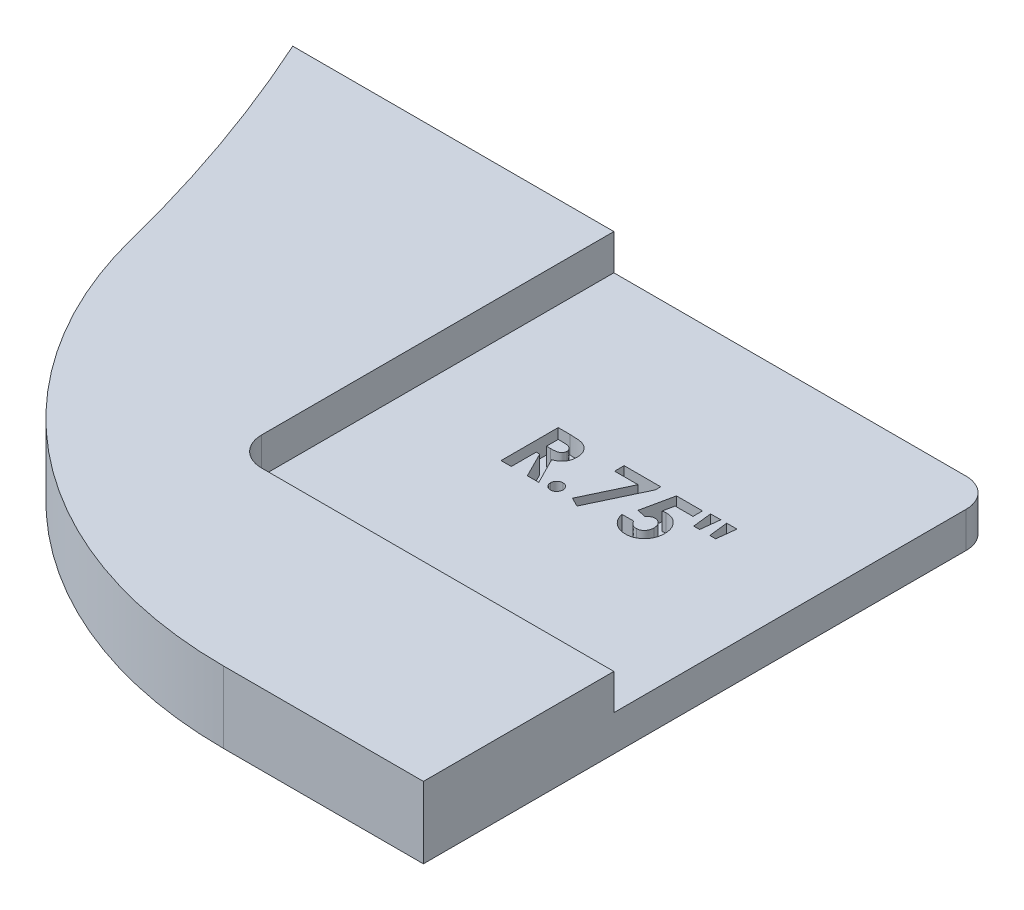
SolidWorks part; units mm, degrees
ref_plane "Front Plane" through (0, 0, 0) normal (0, 0, 1) x (1, 0, 0)
ref_plane "Top Plane" through (0, 0, 0) normal (0, 1, 0) x (1, 0, 0)
ref_plane "Right Plane" through (0, 0, 0) normal (1, 0, 0) x (0, 0, -1)
sketch "Sketch2" plane through (0, 0, 0) normal (0, 1, 0) x (1, 0, 0)
  line L0 (39.9034, 0) -> (66.5271, 0) construction
  line L4 (65.3857, 1.5875) -> (90.7857, 1.5875)
  line L5 (90.7857, 1.5875) -> (90.7857, 26.9875)
  line L6 (90.7857, 26.9875) -> (59.5776, 26.9875)
  arc A0 (65.3857, 1.5875) -> (59.5776, 26.9875) centre (0, 0) ccw
  arc A1 (59.5776, 26.9875) -> (-65.405, 0) centre (0, 0) ccw construction
  arc A2 (-65.405, 0) -> (65.405, 0) centre (0, 0) ccw construction
  arc A3 (65.405, 0) -> (65.3857, 1.5875) centre (0, 0) ccw construction
extrude "Boss-Extrude1" add sketch "Sketch2" along normal mid plane 3.175
fillet "Fillet1" radius 19.05 1 edges at (65.3857, 0, -1.5875)
sketch "Sketch3" plane through (0, 1.5875, 0) normal (0, 1, 0) x (1, 0, 0)
  line L1 (90.7857, 26.9875) -> (73.8524, 26.9875)
  line L2 (90.7857, 26.9875) -> (90.7857, 10.0542)
  line L3 (90.7857, 10.0542) -> (73.8524, 10.0542)
  line L4 (73.8524, 26.9875) -> (73.8524, 10.0542)
  dimension "D1" = 16.9333
extrude "Cut-Extrude1" cut sketch "Sketch3" against normal blind 1.5875
sketch "Sketch4" plane through (0, 0, 0) normal (0, 1, 0) x (1, 0, 0)
  line L0 (73.8524, 18.5208) -> (90.7857, 18.5208) construction
  line L1 (73.8524, 26.9875) -> (73.8524, 10.0542) construction
  line L2 (90.7857, 10.0542) -> (90.7857, 26.9875) construction
  line L3 (73.8524, 17.2508) -> (90.7857, 17.2508) construction
  text T0 "<b>R.75\"</b>\r\n<b> </b>" font "Century Gothic" height 2.54
  dimension "D1" = 1.27
extrude "Cut-Extrude2" cut sketch "Sketch4" against normal blind 0.7937
fillet "Fillet2" radius 1.27 2 edges at (73.8524, 0.7937, -10.0542) (90.7857, -0.7937, -26.9875)
equation "\"AIRFRAME_OD\"= 5.15in"
equation "\"AIRFRAME_ID\"= 4.99in"
equation "\"FLAT_T\"= 0.125in"
equation "\"NOSE_EXP_L\"= 27in"
equation "\"NOSE_SHOULDER_L\"= 5in"
equation "\"MAIN_L\"= 30in"
equation "\"RECO_COUP_L\"= 10in"
equation "\"RECO_SWITCH_L\"= 2in"
equation "\"DROGUE_L\"= 20in"
equation "\"ATS_FORE_COUP_L\"= 5.5in"
equation "\"ATS_AFT_COUP_L\"= 4.5in"
equation "\"LOWER_L\"= 30in"
equation "\"FIN_N\"= 4"
equation "\"CR_AFT_X\"= 0.5in"
equation "\"CR_FORE_X\"= 9.25in"
equation "\"D1@Sketch2\"=\"AIRFRAME_OD\""
equation "\"D2@Sketch2\"=\"FLAT_T\"/2"
equation "\"D1@Boss-Extrude1\"=\"FLAT_T\""
equation "\"COUPLER_OD\"= 4.998in"
equation "\"COUPLER_ID\"= 4.85in"
equation "\"RECO_ROD_X\"= 3.5in"
equation "\"ATS_ROD_X\"= 3.75in"
equation "\"FIN_ROOT\"= 8in"
equation "\"FIN_X\"= 0.75in"
equation "\"MOTOR_OD\"= 3.091in"
equation "\"MOTOR_ID\"= 3.00in"
equation "\"MOTOR_L\"= 14in"
equation "\"MOTOR_LOWER_X\"= 2in"
